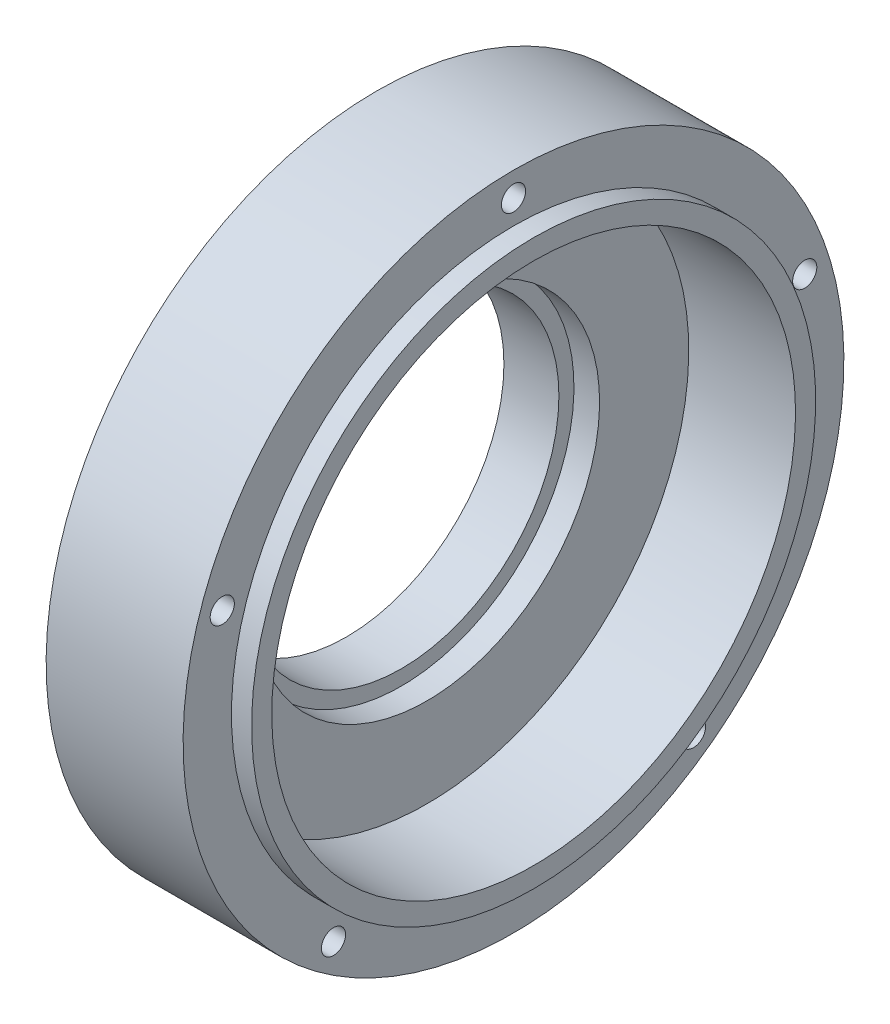
SolidWorks part; units mm, degrees
ref_plane "Front Plane" through (0, 0, 0) normal (0, 0, 1) x (1, 0, 0)
ref_plane "Top Plane" through (0, 0, 0) normal (0, 1, 0) x (1, 0, 0)
ref_plane "Right Plane" through (0, 0, 0) normal (1, 0, 0) x (0, 0, -1)
sketch "Sketch1" plane through (0, 0, 0) normal (0, 0, 1) x (1, 0, 0)
  line L1 (0, -55) -> (0, 55) construction
  line L2 (0, 130) -> (0, 85.73)
  line L10 (-40, 78.25) -> (-40, 88.25)
  line L11 (-40, 88.25) -> (-25, 88.25)
  line L12 (-25, 88.25) -> (-25, 164)
  line L13 (55, 0) -> (-55, 0) construction
  line L14 (100.2885, 0) -> (-44.3603, 0) construction
  line L16 (43, 164) -> (43, 140)
  line L17 (53, 130) -> (53, 140)
  line L18 (53, 140) -> (43, 140)
  line L19 (-25, 164) -> (43, 164)
  line L21 (53, 130) -> (0, 130)
  line L22 (43, 152) -> (-25, 152) construction
  line L23 (0, 85.73) -> (-12.7, 85.73)
  line L24 (-12.7, 85.73) -> (-12.7, 78.25)
  line L25 (-40, 78.25) -> (-12.7, 78.25)
  point P9 (0, 84.6239)
  dimension "D2" = 164
  dimension "D3" = 78.25
  dimension "D4" = 130
  dimension "D5" = 43
  dimension "D6" = 10
  dimension "D7" = 15
  dimension "D8" = 25
  dimension "D9" = 152
  dimension "D10" = 10
  dimension "D11" = 10
  dimension "D12" = 12.7
  dimension "D13" = 85.73
revolve "Revolve1" add sketch "Sketch1" angle 360 about L14
fillet "Fillet3" radius 5 1 edges at (-25, 88.25, 0)
sketch "Sketch2" plane through (43, 0, 0) normal (1, 0, 0) x (0, 0, -1)
  circle A0 centre (0, 152) radius 6
  point P2 (0, 152)
  point P4 (0, 150.4281)
  point P5 (0, 0)
  point P6 (0, 0)
  point P7 (0, 0)
extrude "Cut-Extrude1" cut sketch "Sketch2" against normal up to surface (68 mm away) contours A0 up to face at (-25, 93.25, 0)
pattern_circular "CirPattern1" count 5 over 360 about axis through (0, 0, 0) along (1, 0, 0) of "Cut-Extrude1"
